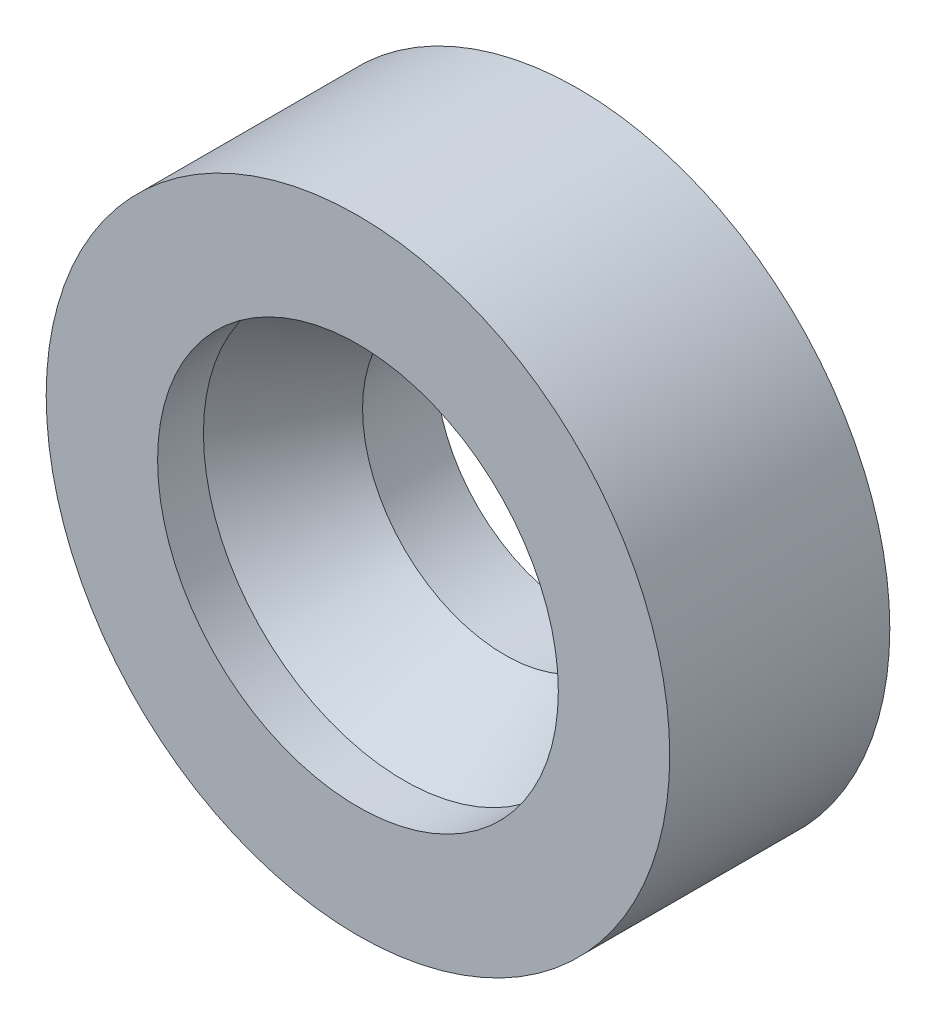
SolidWorks part; units mm, degrees
ref_plane "Front Plane" through (0, 0, 0) normal (0, 0, 1) x (1, 0, 0)
ref_plane "Top Plane" through (0, 0, 0) normal (0, 1, 0) x (1, 0, 0)
ref_plane "Right Plane" through (0, 0, 0) normal (1, 0, 0) x (0, 0, -1)
sketch "Sketch1" plane through (0, 0, 0) normal (0, 0, 1) x (1, 0, 0)
  circle A0 centre (0, 0) radius 3.4
  dimension "D1" = 6.8
extrude "Boss-Extrude1" add sketch "Sketch1" along normal blind 2.4
sketch "Sketch2" plane through (0, 0, 0) normal (0, 0, -1) x (-1, 0, 0)
  circle A0 centre (0, 0) radius 1.55
  dimension "D1" = 3.1
extrude "Cut-Extrude1" cut sketch "Sketch2" against normal blind 0.8
sketch "Sketch3" plane through (0, 0, 0.8) normal (0, 0, -1) x (-1, 0, 0)
  circle A1 centre (0, 0) radius 1.55
  circle A2 centre (0, 0) radius 1.55
  dimension "D1" = 0
extrude "Cut-Extrude2" cut sketch "Sketch3" against normal blind 1.1 draft 30 draft outward yes
sketch "Sketch4" plane through (0, 0, 1.9) normal (0, 0, -1) x (-1, 0, 0)
  circle A1 centre (0, 0) radius 2.1851
  circle A2 centre (0, 0) radius 2.1851
  dimension "D1" = 0
extrude "Cut-Extrude3" cut sketch "Sketch4" against normal up to next
